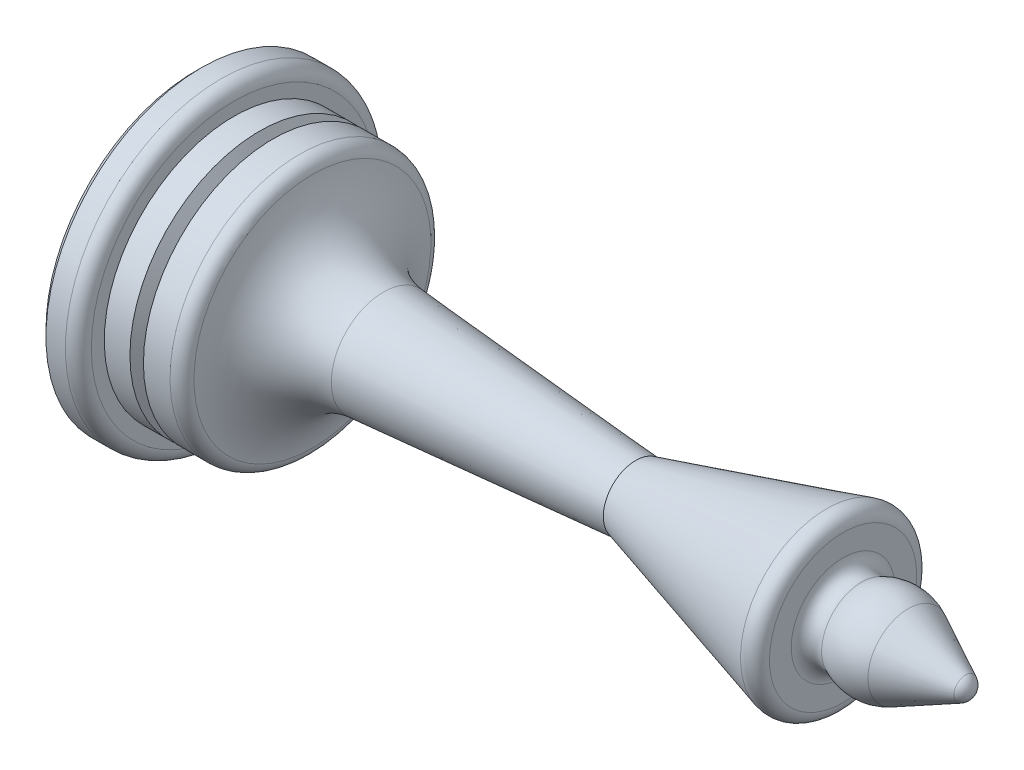
SolidWorks part; units mm, degrees
ref_plane "Front Plane" through (0, 0, 0) normal (0, 0, 1) x (1, 0, 0)
ref_plane "Top Plane" through (0, 0, 0) normal (0, 1, 0) x (1, 0, 0)
ref_plane "Right Plane" through (0, 0, 0) normal (1, 0, 0) x (0, 0, -1)
sketch "Sketch1" plane through (0, 0, 0) normal (0, 0, 1) x (1, 0, 0)
  line L0 (0, 0) -> (0, 11.5)
  line L1 (0.5, 12) -> (2, 12)
  line L2 (3, 11) -> (3, 10)
  line L3 (3, 10) -> (8.0718, 10)
  line L4 (14.5335, 4.0182) -> (30.454, 2.7765)
  line L5 (59.4472, 0.8944) -> (55.0249, 3.1056)
  line L6 (50, 7) -> (50, 4)
  line L7 (0, 0) -> (60, 0)
  line L8 (0, 0) -> (-16.2845, 0) construction
  line L9 (60, 0) -> (60, -26.8947) construction
  line L10 (50, 7) -> (37.4239, 3.463)
  line L11 (30.454, 2.7765) -> (34, 2.5)
  line L12 (34, 2.5) -> (37.4239, 3.463)
  line L13 (28.2223, 27.0457) -> (53.7777, 27.0457) construction
  line L14 (0, 11.5) -> (0.5, 12)
  arc A0 (9.0615, 9.1429) -> (14.5335, 4.0182) centre (15, 10) ccw
  arc A2 (2, 12) -> (3, 11) centre (2, 11) cw
  arc A3 (8.0718, 10) -> (9.0615, 9.1429) centre (8.0718, 9) cw
  arc A4 (50, 4) -> (51.4472, 3.1056) centre (51, 4) ccw
  arc A5 (60, 0) -> (59.4472, 0.8944) centre (59, 0) ccw
  arc A6 (55.0249, 3.1056) -> (51.4472, 3.1056) centre (53.2361, -0.4721) ccw
  point P1 (0, 12)
  point P20 (3, 12)
  point P23 (9, 10)
  point P24 (34, 2.5)
  dimension "D8" = 26
  dimension "D13" = 6
  dimension "D14" = 1
  dimension "D15" = 1
  dimension "D11" = 1
  dimension "D18" = 4
  dimension "D2" = 24
  dimension "D3" = 3
  dimension "D4" = 20
  dimension "D5" = 6
  dimension "D6" = 5
  dimension "D7" = 60
  dimension "D10" = 7
  dimension "D12" = 10
  dimension "D16" = 8
revolve "Revolve1" add sketch "Sketch1" angle 360 about L7
sketch "Sketch2" plane through (0, 0, 0) normal (0, 0, 1) x (1, 0, 0)
  line L0 (4.9794, 10) -> (5.5, 9)
  line L1 (8.0718, 10) -> (3, 10) construction
  line L2 (5.5, 9) -> (6.0206, 10)
  line L3 (4.9794, 10) -> (6.0206, 10)
  line L4 (5.5, 9) -> (5.5, 10) construction
  line L5 (3, -10) -> (3, 10) construction
  line L6 (0, 0) -> (11.1779, 0) construction
  dimension "D1" = 55
  dimension "D2" = 1
  dimension "D3" = 2.5
revolve "Cut-Revolve1" cut sketch "Sketch2" angle 360 about L6
sketch "Sketch3" plane through (0, 0, 0) normal (-1, 0, 0) x (0, 0, 1)
  circle A0 centre (0, 0) radius 6
  dimension "D1" = 12
extrude "Cut-Extrude1" cut sketch "Sketch3" against normal blind 5
fillet "Fillet1" radius 1 1 edges at (50, -7, 0)
